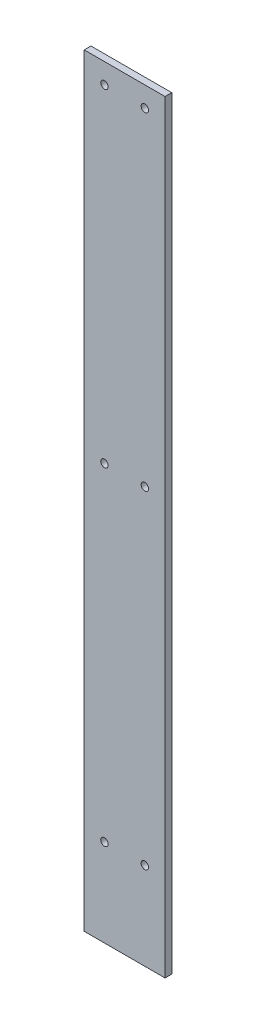
SolidWorks part; units mm, degrees
material "Contreplaqué pin"
ref_plane "Plan de face" through (0, 0, 0) normal (0, 0, 1) x (1, 0, 0)
ref_plane "Plan de dessus" through (0, 0, 0) normal (0, 1, 0) x (1, 0, 0)
ref_plane "Plan de droite" through (0, 0, 0) normal (1, 0, 0) x (0, 0, -1)
sketch "Esquisse1" plane through (0, 0, 0) normal (0, 0, 1) x (1, 0, 0)
  line L0 (15, 567) -> (15, 0) construction
  line L1 (0, 0) -> (60, 0)
  line L2 (0, 0) -> (0, 567)
  line L3 (0, 567) -> (60, 567)
  line L4 (60, 0) -> (60, 567)
  line L5 (45, 567) -> (45, 0) construction
  circle A0 centre (15, 552) radius 2.75
  circle A1 centre (45, 552) radius 2.75
  circle A2 centre (45, 308.5) radius 2.75
  circle A3 centre (15, 308.5) radius 2.75
  circle A4 centre (45, 65) radius 2.75
  circle A5 centre (15, 65) radius 2.75
  dimension "D5" = 5.5
  dimension "D1" = 567
  dimension "D2" = 60
  dimension "D3" = 15
  dimension "D4" = 15
  dimension "D6" = 15
  dimension "D7" = 243.5
  dimension "D8" = 243.5
extrude "Boss.-Extru.1" add sketch "Esquisse1" along normal blind 5
